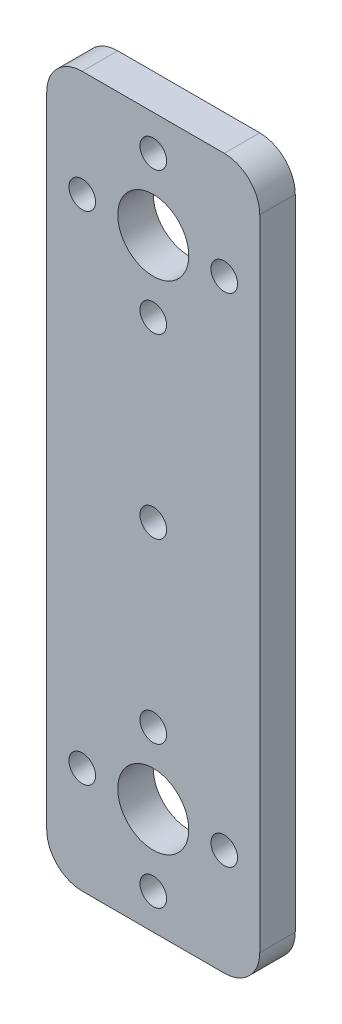
SolidWorks part; units mm, degrees
ref_plane "Front Plane" through (0, 0, 0) normal (0, 0, 1) x (1, 0, 0)
ref_plane "Top Plane" through (0, 0, 0) normal (0, 1, 0) x (1, 0, 0)
ref_plane "Right Plane" through (0, 0, 0) normal (1, 0, 0) x (0, 0, -1)
sketch "Sketch1" plane through (0, 0, 0) normal (0, 0, 1) x (1, 0, 0)
  line L1 (-57.2967, 34.9503) -> (-33.2967, 34.9503)
  line L2 (-57.2967, 34.9503) -> (-57.2967, -45.0497)
  line L3 (-57.2967, -45.0497) -> (-33.2967, -45.0497)
  line L4 (-33.2967, 34.9503) -> (-33.2967, -45.0497)
  dimension "D1" = 80
  dimension "D2" = 24
extrude "Boss-Extrude1" add sketch "Sketch1" along normal blind 4 contours L2 L3 L4 L1
sketch "Sketch2" plane through (0, 0, 4) normal (0, 0, 1) x (1, 0, 0)
  circle A0 centre (-45.2967, -33.0497) radius 4
  circle A1 centre (-37.2967, -33.0497) radius 1.5
  circle A2 centre (-45.2967, -41.0497) radius 1.5
  circle A3 centre (-45.2967, -33.0497) radius 4
  circle A4 centre (-53.2967, -33.0497) radius 1.5
  circle A5 centre (-45.2967, -33.0497) radius 4
  circle A6 centre (-45.2967, -25.0497) radius 1.5
  circle A7 centre (-45.2967, -33.0497) radius 4
  circle A18 centre (-45.2967, 30.9503) radius 1.5
  circle A19 centre (-37.2967, 22.9503) radius 1.5
  circle A20 centre (-45.2967, 14.9503) radius 1.5
  circle A21 centre (-53.2967, 22.9503) radius 1.5
  circle A22 centre (-45.2967, 22.9503) radius 4
  point P21 (-45.2967, -17.0497)
extrude "Cut-Extrude1" cut sketch "Sketch2" against normal blind 4 contours A6 | A0 | A1 | A2 | A4 | A21 | A18 | A22 | A19 | A20
fillet "Fillet1" radius 4 4 edges at (-57.2967, -45.0497, 2) (-33.2967, -45.0497, 2) (-57.2967, 34.9503, 2) (-33.2967, 34.9503, 2)
sketch "Sketch3" plane through (0, 0, 4) normal (0, 0, 1) x (1, 0, 0)
  circle A0 centre (-45.2967, -5.0497) radius 1.5
  circle A1 centre (-45.2967, 22.9503) radius 4 construction
  dimension "D1" = 28
extrude "Cut-Extrude2" cut sketch "Sketch3" against normal blind 4 contours A0
